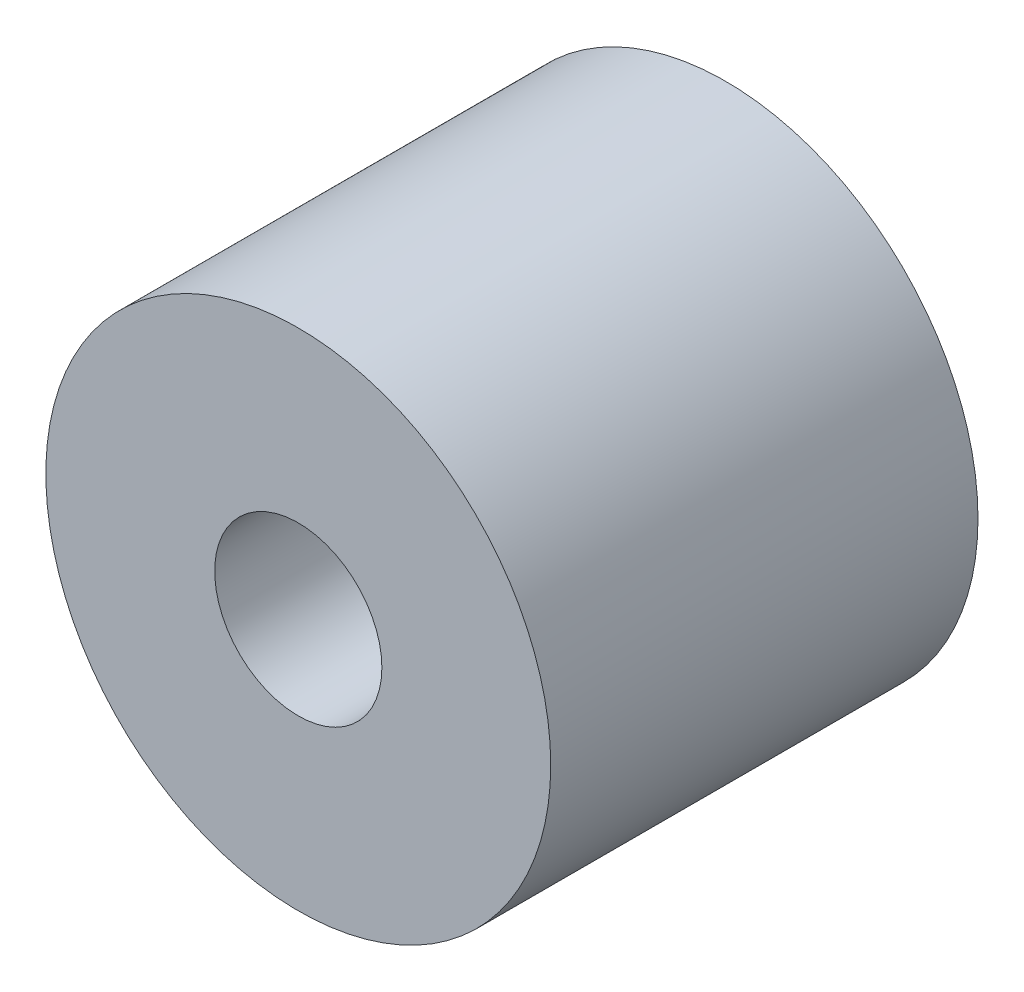
SolidWorks part; units mm, degrees
ref_plane "Front Plane" through (0, 0, 0) normal (0, 0, 1) x (1, 0, 0)
ref_plane "Top Plane" through (0, 0, 0) normal (0, 1, 0) x (1, 0, 0)
ref_plane "Right Plane" through (0, 0, 0) normal (1, 0, 0) x (0, 0, -1)
sketch "Sketch1" plane through (0, 0, 0) normal (0, 0, 1) x (1, 0, 0)
  circle A0 centre (0, 0) radius 39.116
  circle A1 centre (0, 0) radius 118.11
  dimension "D1" = 78.232
  dimension "D2" = 236.22
extrude "Boss-Extrude1" add sketch "Sketch1" along normal blind 199.898
sketch3d "3DSketch1"
  line L0 (0, 0, 199.898) -> (0, 0, 0) construction
  line L1 (0, 0, 199.898) -> (0, 0, 0) construction
  line L2 (0, 0, 199.898) -> (0, 0, 0) construction
  point P7 (0, 0, 99.949)
ref_plane "Plane1" through (0, 0, 99.949) normal (0, 0, 1) x (1, 0, 0)
